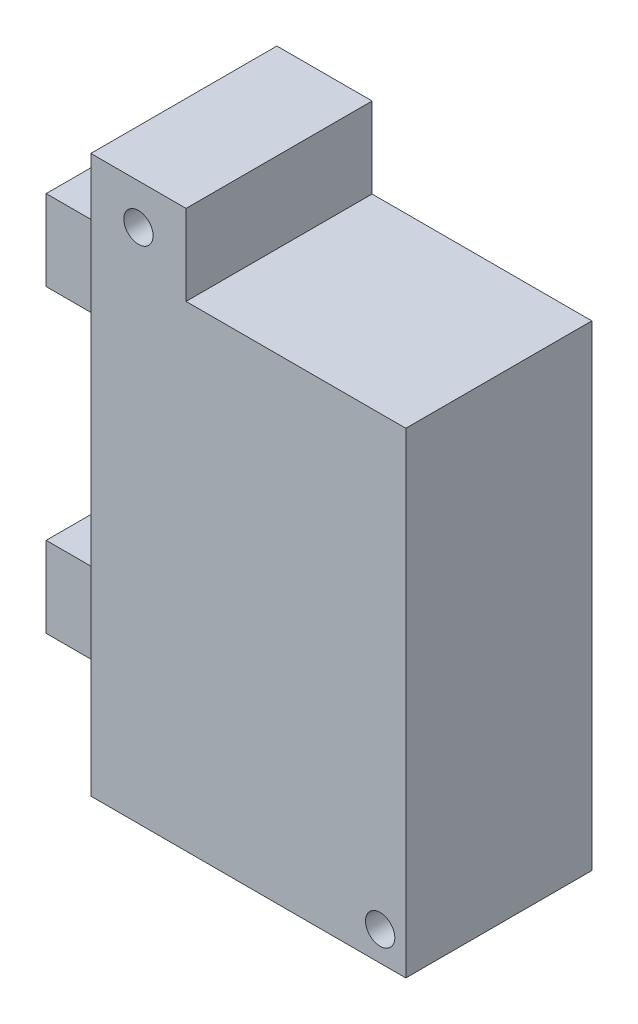
SolidWorks part; units mm, degrees
ref_plane "Alzado" through (0, 0, 0) normal (0, 0, 1) x (1, 0, 0)
ref_plane "Planta" through (0, 0, 0) normal (0, 1, 0) x (1, 0, 0)
ref_plane "Vista lateral" through (0, 0, 0) normal (1, 0, 0) x (0, 0, -1)
sketch "Croquis1" plane through (0, 0, 0) normal (0, 0, 1) x (1, 0, 0)
  line L0 (13, 65) -> (43, 65)
  line L1 (0, 0) -> (43, 0)
  line L2 (0, 0) -> (0, 65)
  line L3 (0, 65) -> (43, 65) construction
  line L4 (43, 0) -> (43, 65)
  line L5 (0, 0) -> (43, 65) construction
  line L6 (0, 65) -> (43, 0) construction
  line L7 (0, 65) -> (13, 65) construction
  line L8 (0, 65) -> (0, 76)
  line L9 (0, 76) -> (13, 76)
  line L10 (13, 65) -> (13, 76)
  line L11 (0, 65) -> (13, 76) construction
  line L12 (0, 76) -> (13, 65) construction
  circle A0 centre (39.5, 4) radius 2
  circle A1 centre (6.5, 70.5) radius 2
  point P4 (21.5, 32.5)
  point P10 (6.5, 70.5)
  point P14 (0, 0)
  dimension "D5" = 4
  dimension "D1" = 43
  dimension "D2" = 65
  dimension "D3" = 13
  dimension "D4" = 76
  dimension "D6" = 3.5
  dimension "D7" = 4
extrude "Saliente-Extruir1" add sketch "Croquis1" along normal mid plane 25.4
sketch "Croquis2" plane through (0, 0, 0) normal (0, 0, 1) x (1, 0, 0)
  line L0 (0, 76) -> (0, 0) construction
  line L1 (0, 64) -> (-10.3, 64)
  line L2 (0, 64) -> (0, 53)
  line L3 (0, 53) -> (-10.3, 53)
  line L4 (-10.3, 64) -> (-10.3, 53)
  line L5 (0, 64) -> (-10.3, 53) construction
  line L6 (0, 53) -> (-10.3, 64) construction
  line L7 (0, 0) -> (43, 0) construction
  line L8 (0, 12) -> (-10.3, 12)
  line L9 (0, 12) -> (0, 23)
  line L10 (0, 23) -> (-10.3, 23)
  line L11 (-10.3, 12) -> (-10.3, 23)
  line L12 (0, 12) -> (-10.3, 23) construction
  line L13 (0, 23) -> (-10.3, 12) construction
  point P4 (-5.15, 58.5)
  point P11 (-5.15, 17.5)
  dimension "D1" = 11
  dimension "D2" = 10.3
  dimension "D3" = 12
  dimension "D4" = 30
extrude "Saliente-Extruir2" add sketch "Croquis2" along normal mid plane 17
sketch "Croquis3" plane through (-10.3, 0, 0) normal (-1, 0, 0) x (0, 0, 1)
  line L0 (0, 0) -> (0, 50000) construction
  line L1 (-8.5, 64) -> (8.5, 53) construction
  line L2 (-8.5, 23) -> (8.5, 12) construction
  circle A0 centre (0, 58.5) radius 3
  circle A1 centre (0, 17.5) radius 3
  dimension "D1" = 6
extrude "Cortar-Extruir1" cut sketch "Croquis3" against normal blind 9.5
